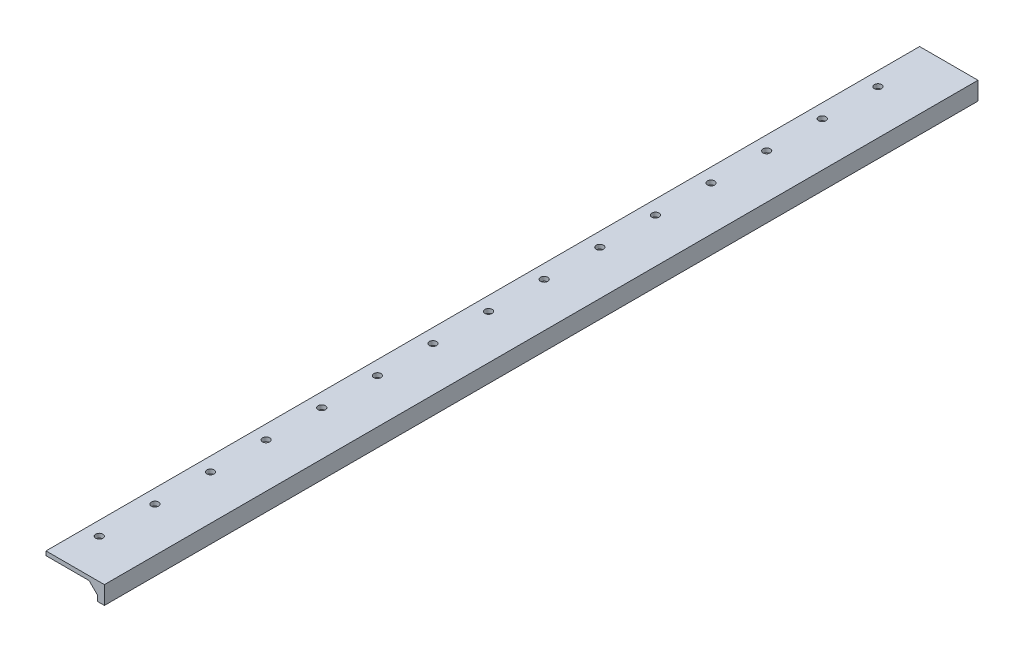
SolidWorks part; units mm, degrees
ref_plane "정면" through (0, 0, 0) normal (0, 0, 1) x (1, 0, 0)
ref_plane "윗면" through (0, 0, 0) normal (0, 1, 0) x (1, 0, 0)
ref_plane "우측면" through (0, 0, 0) normal (1, 0, 0) x (0, 0, -1)
sketch "스케치1" plane through (0, 0, 0) normal (0, 1, 0) x (1, 0, 0)
  line L1 (-37, 0) -> (0, 0)
  line L2 (-37, 0) -> (-37, -628.32)
  line L3 (-37, -628.32) -> (0, -628.32)
  line L4 (0, 0) -> (0, -628.32)
  line L5 (-37, 0) -> (0, -628.32) construction
  line L6 (-37, -628.32) -> (0, 0) construction
  point P4 (-18.5, -314.16)
  dimension "D1" = 37
  dimension "D2" = 628.32
extrude "보스-돌출1" add sketch "스케치1" along normal blind 3 contours L1 L4 L3 L2
sketch "스케치2" plane through (0, 0, 0) normal (0, -1, 0) x (1, 0, 0)
  line L0 (-37, 628.32) -> (0, 628.32) construction
  line L1 (0, 0) -> (5, 0)
  line L2 (0, 0) -> (0, 628.32)
  line L3 (0, 628.32) -> (5, 628.32)
  line L4 (5, 0) -> (5, 628.32)
  line L5 (0, 0) -> (5, 628.32) construction
  line L6 (0, 628.32) -> (5, 0) construction
  point P4 (2.5, 314.16)
  dimension "D1" = 5
extrude "보스-돌출2" add sketch "스케치2" along normal blind 10 and the other way blind 3
sketch "스케치3" plane through (0, 0, 0) normal (0, -1, 0) x (1, 0, 0)
  line L0 (-37, 0) -> (-37, 628.32) construction
  line L1 (-37, 0) -> (0, 0) construction
  circle A0 centre (-27, 40) radius 2.6
  circle A1 centre (-27, 80) radius 2.6
  circle A2 centre (-27, 120) radius 2.6
  circle A3 centre (-27, 160) radius 2.6
  circle A4 centre (-27, 200) radius 2.6
  circle A5 centre (-27, 240) radius 2.6
  circle A6 centre (-27, 280) radius 2.6
  circle A7 centre (-27, 320) radius 2.6
  circle A8 centre (-27, 360) radius 2.6
  circle A9 centre (-27, 400) radius 2.6
  circle A10 centre (-27, 440) radius 2.6
  circle A11 centre (-27, 480) radius 2.6
  circle A12 centre (-27, 520) radius 2.6
  circle A13 centre (-27, 560) radius 2.6
  circle A14 centre (-27, 600) radius 2.6
  circle A15 centre (-27, 640) radius 2.6
  dimension "D1" = 5.2
  dimension "D2" = 10
  dimension "D3" = 40
extrude "컷-돌출1" cut sketch "스케치3" against normal blind 10
sketch "스케치4" plane through (0, 0, 628.32) normal (0, 0, 1) x (1, 0, 0)
  line L6 (0, 0) -> (0, -6)
  line L7 (0, 0) -> (0, -10) construction
  line L8 (0, -6) -> (-6, 0)
  line L9 (-37, 0) -> (0, 0) construction
  line L10 (-6, 0) -> (0, 0)
  dimension "D1" = 6
  dimension "D2" = 6
extrude "보스-돌출3" add sketch "스케치4" against normal up to vertex (628.32 mm away) up to point (0, 0, 0)
